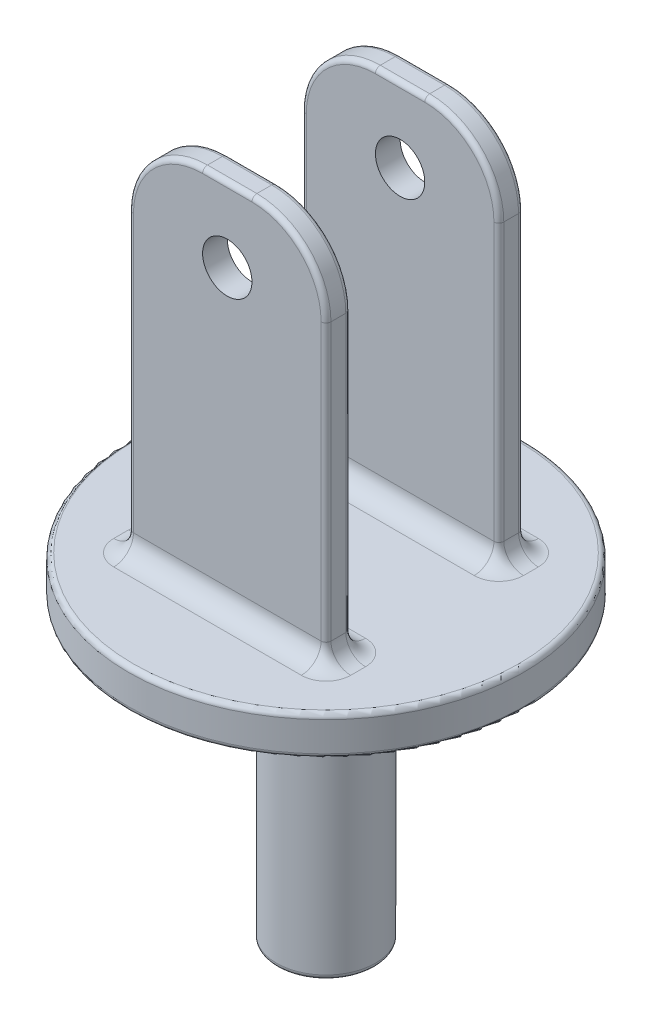
SolidWorks part; units mm, degrees
ref_plane "Front Plane" through (0, 0, 0) normal (0, 0, 1) x (1, 0, 0)
ref_plane "Top Plane" through (0, 0, 0) normal (0, 1, 0) x (1, 0, 0)
ref_plane "Right Plane" through (0, 0, 0) normal (1, 0, 0) x (0, 0, -1)
sketch "Sketch1" plane through (0, 0, 0) normal (0, 1, 0) x (1, 0, 0)
  circle A0 centre (0, 0) radius 40
  dimension "D1" = 80
extrude "Boss-Extrude1" add sketch "Sketch1" along normal blind 8 contours A0
sketch "Sketch2" plane through (0, 8, 0) normal (0, 1, 0) x (1, 0, 0)
  line L0 (0, 0) -> (0, 17.5)
  line L1 (20, 20) -> (-20, 15)
  line L2 (-20, 20) -> (20, 20)
  line L3 (-20, 20) -> (-20, 15)
  line L4 (-20, 15) -> (20, 15)
  line L5 (20, 20) -> (20, 15)
  line L6 (-20, 20) -> (20, 15)
  point P7 (0, 17.5)
  dimension "D1" = 15
  dimension "D2" = 40
  dimension "D3" = 5
extrude "Boss-Extrude4" add sketch "Sketch2" along normal blind 75 contours L1 L6 L5 | L2 L6 L1 | L6 L0 L4 | L1 L4 L0 | L6 L3 L1
fillet "Fillet4" radius 15 2 edges at (20, 83, -17.5) (-20, 83, -17.5)
fillet "Fillet6" radius 1 5 edges at (20, 38, -15) (15.6066, 78.6066, -15) (0, 83, -15) (-15.6066, 78.6066, -15) (-20, 38, -15)
fillet "Fillet8" radius 1 5 edges at (-20, 38, -20) (20, 38, -20) (15.6066, 78.6066, -20) (0, 83, -20) (-15.6066, 78.6066, -20)
fillet "Fillet9" radius 4 8 edges at (-19.7071, 8, -15.2929) (-20, 8, -17.5) (-19.7071, 8, -19.7071) (0, 8, -20) (19.7071, 8, -19.7071) (20, 8, -17.5) (19.7071, 8, -15.2929) (0, 8, -15)
mirror "Mirror6" about plane through (0, 0, 0) normal (0, 0, 1) of "Fillet9", "Fillet6", "Fillet8", "Fillet4", "Boss-Extrude4"
sketch "Sketch3" plane through (0, 0, -20) normal (0, 0, -1) x (-1, 0, 0)
  line L0 (-5, 83) -> (5, 83) construction
  line L1 (0, 82) -> (0, 12)
  line L2 (5, 82) -> (-5, 82) construction
  line L3 (-19, 12) -> (19, 12) construction
  circle A0 centre (0, 68) radius 5
  dimension "D1" = 10
  dimension "D2" = 15
extrude "Cut-Extrude1" cut sketch "Sketch3" against normal blind 76 contours L1 A0 | L1 A0
sketch "Sketch5" plane through (0, 0, 0) normal (0, -1, 0) x (1, 0, 0)
  circle A0 centre (0, 0) radius 7.5
  circle A1 centre (0, 0) radius 10
  dimension "D1" = 15
  dimension "D2" = 20
extrude "Boss-Extrude5" add sketch "Sketch5" along normal blind 60
fillet "Fillet10" radius 1 1 edges at (0, -60, -10)
fillet "Fillet11" radius 1 2 edges at (0, 8, 40) (0, 0, 40)
